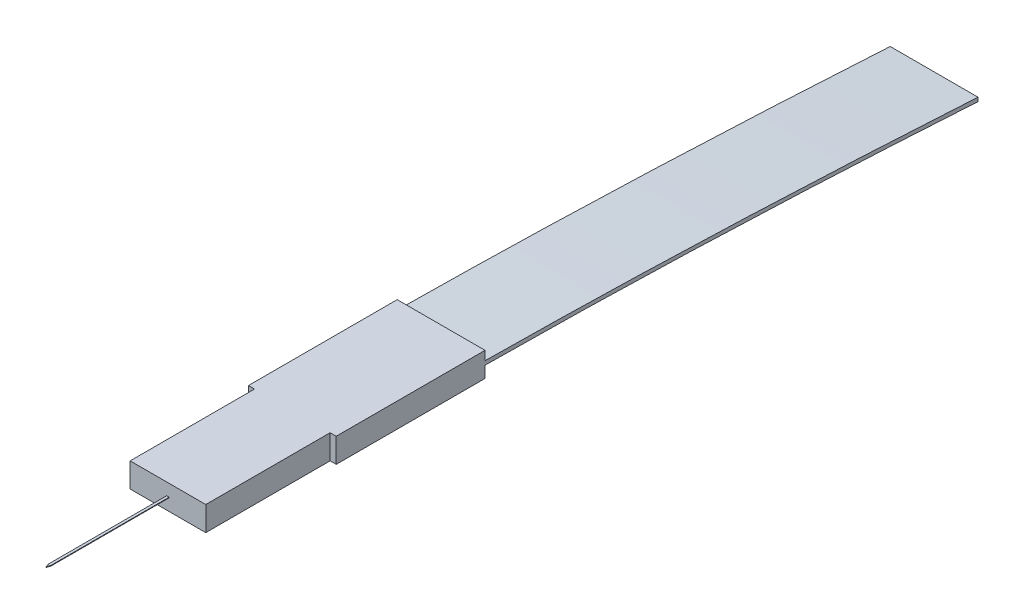
SolidWorks part; units mm, degrees
ref_plane "Front Plane" through (0, 0, 0) normal (0, 0, 1) x (1, 0, 0)
ref_plane "Top Plane" through (0, 0, 0) normal (0, 1, 0) x (1, 0, 0)
ref_plane "Right Plane" through (0, 0, 0) normal (1, 0, 0) x (0, 0, -1)
sketch "Sketch1" plane through (0, 0, 0) normal (0, 1, 0) x (1, 0, 0)
  line L0 (-3.1, -6.1) -> (3.1, -6.1)
  line L1 (-3.6, -6.1) -> (3.6, -6.1)
  line L2 (-3.6, -6.1) -> (-3.6, 6.1)
  line L3 (-3.6, 6.1) -> (3.6, 6.1)
  line L4 (3.6, -6.1) -> (3.6, 6.1)
  line L5 (0, 6.1) -> (0, -6.1) construction
  line L6 (-3.6, 0) -> (3.6, 0) construction
  line L8 (-3.1, -6.1) -> (3.1, -6.1)
  line L9 (-3.1, -6.1) -> (-3.1, -16.3)
  line L10 (-3.1, -16.3) -> (3.1, -16.3)
  line L11 (3.1, -6.1) -> (3.1, -16.3)
  point P0 (0, 0)
  point P7 (0, -6.1)
  dimension "D1" = 7.2
  dimension "D2" = 12.2
  dimension "D3" = 10.2
extrude "Boss-Extrude1" add sketch "Sketch1" along normal blind 2 contours L1 L4 L3 L2 L0 | L11 L0 L9 L10
sketch "Sketch2" plane through (0, 0, -6.1) normal (0, 0, -1) x (-1, 0, 0)
  line L0 (0, 0) -> (0, 2) construction
  line L1 (3.6, 0) -> (-3.6, 0) construction
  line L2 (3.6, 2) -> (-3.6, 2) construction
  line L4 (-3.55, 0.8732) -> (3.55, 0.8732)
  line L5 (-3.55, 0.8732) -> (-3.55, 1.1268)
  line L6 (-3.55, 1.1268) -> (3.55, 1.1268)
  line L7 (3.55, 0.8732) -> (3.55, 1.1268)
  line L8 (0, 1.1268) -> (0, 0.8732) construction
  line L9 (-3.55, 1) -> (3.55, 1) construction
  point P6 (0, 1)
  dimension "D1" = 7.1
extrude "Boss-Extrude2" [suppressed] add sketch "Sketch2" along normal blind 30
sketch "Sketch3" plane through (0, 0, 16.3) normal (0, 0, 1) x (1, 0, 0)
  line L0 (0, 0) -> (0, 2) construction
  line L1 (-3.1, 2) -> (3.1, 2) construction
  line L3 (-0.1, 0.975) -> (0.1, 0.975)
  line L4 (-0.1, 0.975) -> (-0.1, 1.025)
  line L5 (-0.1, 1.025) -> (0.1, 1.025)
  line L6 (0.1, 0.975) -> (0.1, 1.025)
  line L7 (0, 1.025) -> (0, 0.975) construction
  line L8 (-0.1, 1) -> (0.1, 1) construction
  point P5 (0, 1)
  dimension "D1" = 0.05
  dimension "D2" = 0.2
extrude "Boss-Extrude3" add sketch "Sketch3" along normal blind 10
sketch "Sketch4" plane through (0, 0.975, 0) normal (0, -1, 0) x (1, 0, 0)
  line L0 (0, 26.3) -> (0, 26) construction
  line L1 (-0.1, 26.3) -> (0.1, 26.3) construction
  line L2 (-0.1, 26) -> (0.1, 26) construction
  line L3 (-0.1, 26.3) -> (-0.1, 16.3) construction
  line L4 (0.1, 26.3) -> (0.1, 16.3) construction
  line L5 (-0.1, 26) -> (0, 26.3)
  line L6 (0, 26.3) -> (0.1, 26)
  line L7 (-0.1, 26) -> (-0.1, 26.3)
  line L8 (-0.1, 26.3) -> (0.1, 26.3)
  line L9 (0.1, 26.3) -> (0.1, 26)
  line M3 (0.1, 16.3) -> (0.1, 26.3)
  line M4 (0.1, 26.3) -> (-0.1, 26.3)
  line M5 (-0.1, 26.3) -> (-0.1, 16.3)
  dimension "D1" = 0.3
extrude "Cut-Extrude1" cut sketch "Sketch4" against normal up to surface (0.05 mm away) contours L6 M4 M3 | L5 M5 M4 up to face at (0, 1.025, 21.3)
sketch "Sketch5" plane through (3.6, 0, 0) normal (1, 0, 0) x (0, 0, -1)
  line L1 (6.1, 2) -> (6.1, 0) construction
  line L2 (6.1, 1.2618) -> (6.1, 0.9423)
  line L3 (46.5259, -0.2347) -> (46.5259, -0.5541)
  spline S0 degree 2 poles (6.1, 0.9423) (24.5183, 0.8103) (46.5259, -0.5541) knots 0 0 0 1 1 1
  spline S1 degree 2 poles (6.1, 1.2618) (24.5624, 1.0834) (46.5259, -0.2347) knots 0 0 0 1 1 1
  point P2 (0, 0)
  point P3 (0, 0)
  point P4 (36.9103, -1.4723)
  point P5 (0, 0)
  point P6 (0, 0)
  point P9 (46.5483, 0.2861)
  point P12 (0, 0)
  point P13 (46.1748, -0.5746)
  point P14 (0, 0)
  point P15 (46.5259, -0.2347)
extrude "Boss-Extrude4" add sketch "Sketch5" against normal blind 7.2
